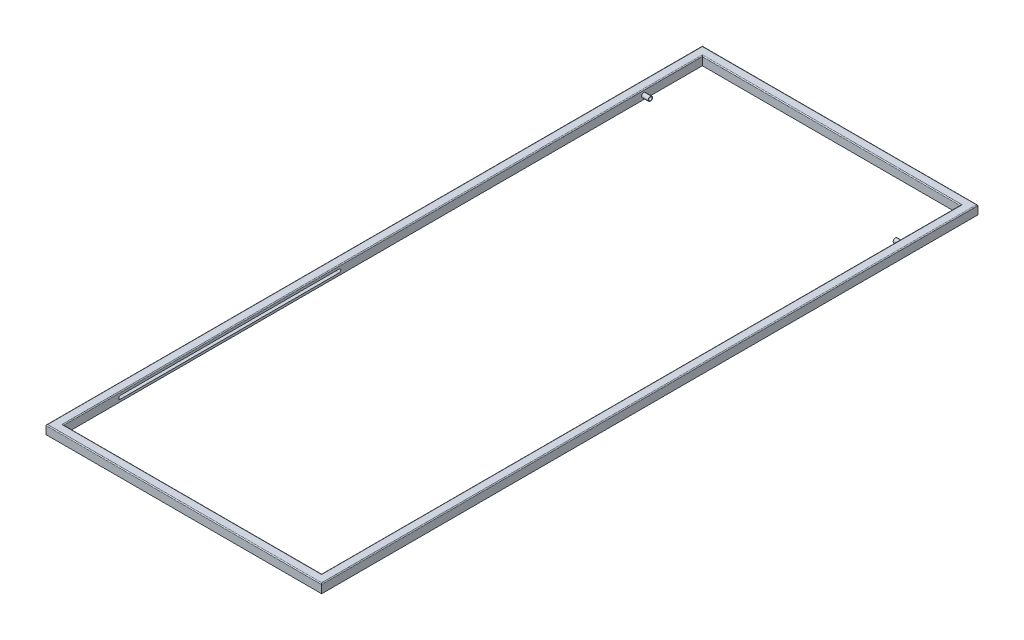
SolidWorks part; units mm, degrees
ref_plane "Alzado" through (0, 0, 0) normal (0, 0, 1) x (1, 0, 0)
ref_plane "Planta" through (0, 0, 0) normal (0, 1, 0) x (1, 0, 0)
ref_plane "Vista lateral" through (0, 0, 0) normal (1, 0, 0) x (0, 0, -1)
sketch "Croquis1" plane through (0, 0, 0) normal (0, 1, 0) x (1, 0, 0)
  line L0 (0, 750) -> (0, -750) construction
  line L1 (-315, -750) -> (315, -750)
  line L2 (-315, -750) -> (-315, 750)
  line L3 (-315, 750) -> (315, 750)
  line L4 (315, -750) -> (315, 750)
  line L5 (-315, -750) -> (315, 750) construction
  line L6 (-315, 750) -> (315, -750) construction
  line L7 (-295, -730) -> (295, -730)
  line L8 (-295, -730) -> (-295, 730)
  line L9 (-295, 730) -> (295, 730)
  line L10 (295, -730) -> (295, 730)
  line L11 (-295, -730) -> (295, 730) construction
  line L12 (-295, 730) -> (295, -730) construction
  line L13 (-315, 0) -> (315, 0) construction
  line L14 (-295, 730) -> (-315, 750) construction
  point P0 (0, 0)
  point P6 (0, 0)
  dimension "D1" = 630
  dimension "D2" = 1500
  dimension "D3" = 590
  dimension "D4" = 1460
extrude "Saliente-Extruir1" add sketch "Croquis1" along normal blind 20
sketch "Croquis2" plane through (0, 0, 0) normal (0, -1, 0) x (1, 0, 0)
  line L0 (-315, 750) -> (-295, 730) construction
  line L1 (0, 750) -> (0, -750) construction
  line L2 (-315, 750) -> (315, 750) construction
  line L3 (315, -750) -> (-315, -750) construction
  line L4 (-315, 0) -> (315, 0) construction
  line L5 (-315, -750) -> (-315, 750) construction
  line L6 (315, 750) -> (315, -750) construction
  circle A0 centre (-305, 740) radius 5
  circle A1 centre (305, 740) radius 5
  circle A2 centre (305, -740) radius 5
  circle A3 centre (-305, -740) radius 5
  dimension "D1" = 10
extrude "Cortar-Extruir1" cut sketch "Croquis2" against normal blind 15
fillet "Redondeo1" radius 2 8 edges at (0, 20, -730) (0, 20, -750) (295, 20, 0) (315, 20, 0) (0, 20, 730) (0, 20, 750) (-295, 20, 0) (-315, 20, 0)
sketch "Croquis4" plane through (295, 0, 0) normal (-1, 0, 0) x (0, 0, 1)
  line L0 (0, 18) -> (0, 0) construction
  line L1 (730, 18) -> (-730, 18) construction
  line L2 (730, 0) -> (-730, 0) construction
  line L3 (0, 12.75) -> (600, 12.75)
  line L4 (0, 5.25) -> (600, 5.25)
  line L5 (0, 9) -> (100, 9) construction
  line L6 (100, 9) -> (100, 12.75) construction
  line L7 (100, 12.75) -> (100, 5.25) construction
  line L8 (100, 5.25) -> (100, 12.75)
  arc A0 (600, 12.75) -> (600, 5.25) centre (600, 9) cw
  arc A1 (100, 12.75) -> (100, 5.25) centre (100, 9) ccw
  point P8 (0, 9)
  dimension "D1" = 3.75
  dimension "D2" = 600
  dimension "D3" = 3.75
  dimension "D4" = 600
  dimension "D5" = 100
extrude "Cortar-Extruir2" cut sketch "Croquis4" against normal blind 15 and the other way blind 605 contours A0 L3 L8 L4 | L8 A1
sketch "Croquis5" plane through (295, 0, 0) normal (-1, 0, 0) x (0, 0, 1)
  line L0 (0, 0) -> (0, 18) construction
  line L1 (730, 18) -> (-730, 18) construction
  line L2 (0, 9) -> (-596.25, 9) construction
  circle A0 centre (-596.25, 9) radius 5
  circle A1 centre (-596.25, 9) radius 3.75
  dimension "D2" = 10
  dimension "D3" = 7.5
  dimension "D1" = 596.25
extrude "Saliente-Extruir2" add sketch "Croquis5" along normal blind 15
mirror "Simetría1" about plane through (0, 0, 0) normal (1, 0, 0) of "Saliente-Extruir2"
scale "Escala1" scale about origin uniform scaling yes scale factor 1.3
